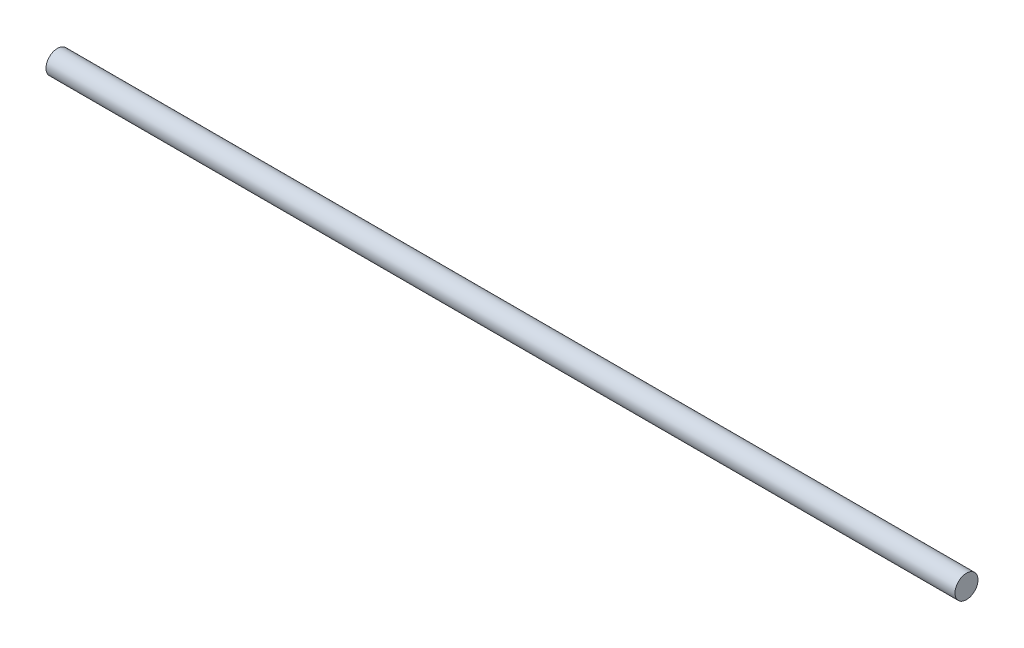
SolidWorks part; units mm, degrees
ref_plane "Front Plane" through (0, 0, 0) normal (0, 0, 1) x (1, 0, 0)
ref_plane "Top Plane" through (0, 0, 0) normal (0, 1, 0) x (1, 0, 0)
ref_plane "Right Plane" through (0, 0, 0) normal (1, 0, 0) x (0, 0, -1)
sketch "Sketch1" plane through (0, 0, 0) normal (1, 0, 0) x (0, 0, -1)
  circle A0 centre (0, 0) radius 6.35
  dimension "D1" = 12.7
extrude "Boss-Extrude1" add sketch "Sketch1" along normal blind 501.3
